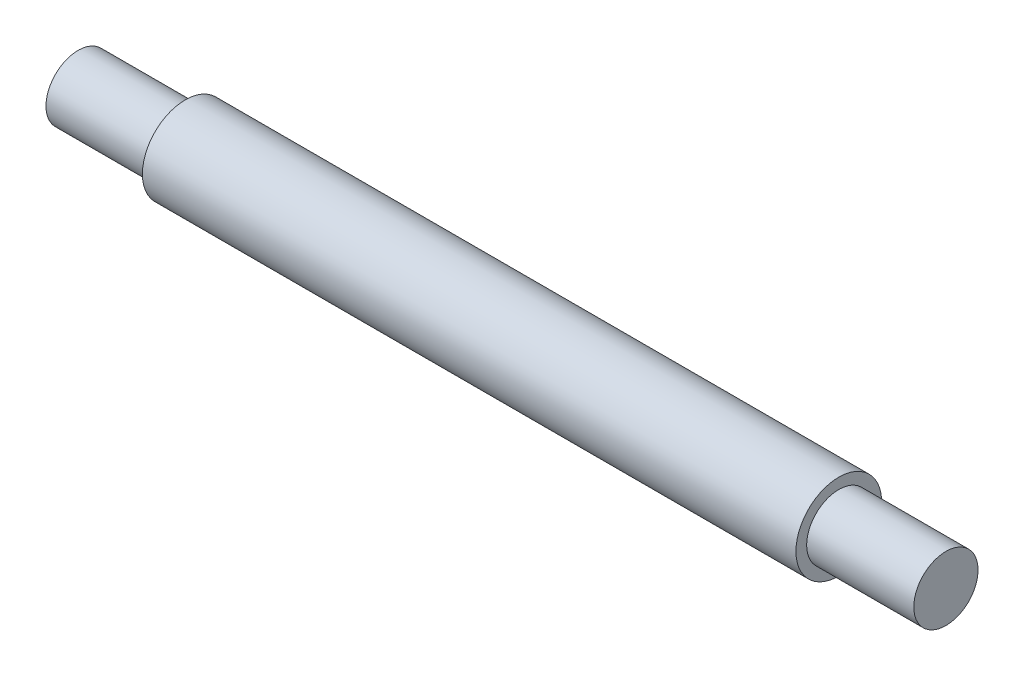
SolidWorks part; units mm, degrees
material "镀铬不锈钢"
ref_plane "前视基准面" through (0, 0, 0) normal (0, 0, 1) x (1, 0, 0)
ref_plane "上视基准面" through (0, 0, 0) normal (0, 1, 0) x (1, 0, 0)
ref_plane "右视基准面" through (0, 0, 0) normal (1, 0, 0) x (0, 0, -1)
sketch "草图1" plane through (0, 0, 0) normal (0, 0, 1) x (1, 0, 0)
  line L0 (-73.231, 0) -> (78.4949, 0) construction
  line L1 (-40.5, 0) -> (40.5, 0)
  line L2 (40.5, 0) -> (40.5, 3)
  line L3 (40.5, 3) -> (30.5, 3)
  line L4 (30.5, 3) -> (30.5, 4)
  line L5 (30.5, 4) -> (-30.5, 4)
  line L6 (-30.5, 4) -> (-30.5, 3)
  line L7 (-30.5, 3) -> (-40.5, 3)
  line L8 (-40.5, 3) -> (-40.5, 0)
  line L9 (0, -17.4175) -> (0, 38.0089) construction
  dimension "D1" = 61
  dimension "D2" = 10
  dimension "D3" = 4
  dimension "D4" = 3
revolve "旋转1" add sketch "草图1" angle 360 about L0
cosmetic thread "装饰螺纹线1" parameters "D1"=10, "D2"=4.917
cosmetic thread "装饰螺纹线2" parameters "D1"=10, "D2"=4.917
